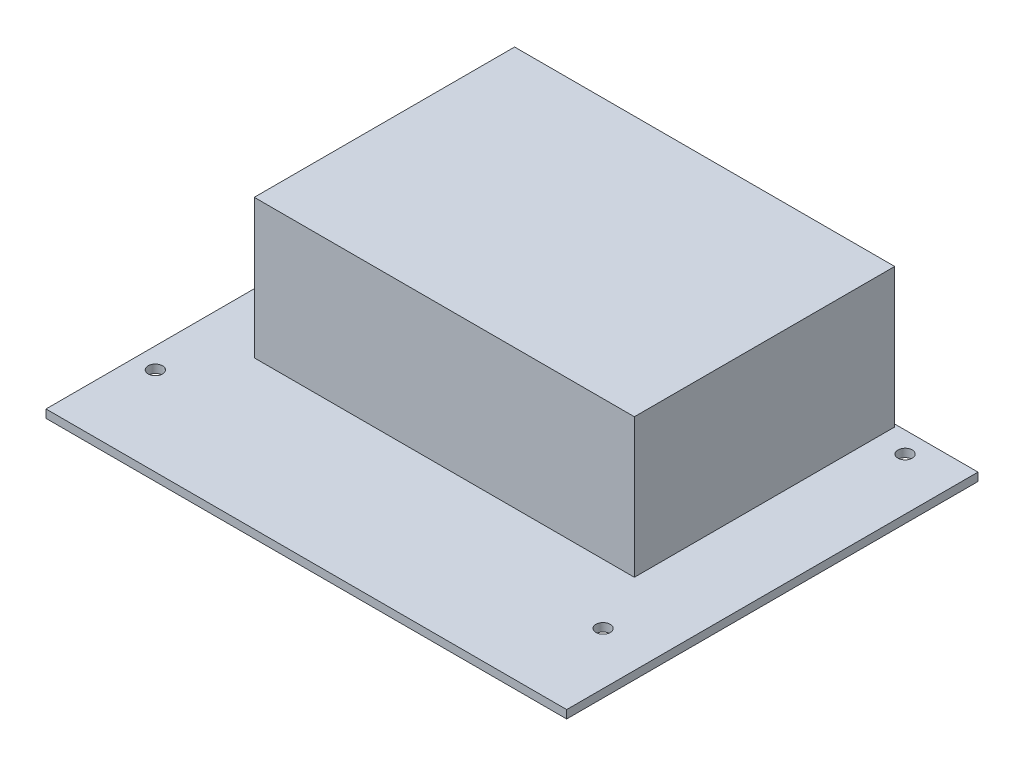
SolidWorks part; units mm, degrees
ref_plane "Front Plane" through (0, 0, 0) normal (0, 0, 1) x (1, 0, 0)
ref_plane "Top Plane" through (0, 0, 0) normal (0, 1, 0) x (1, 0, 0)
ref_plane "Right Plane" through (0, 0, 0) normal (1, 0, 0) x (0, 0, -1)
sketch "Sketch1" plane through (0, 0, 0) normal (0, 1, 0) x (1, 0, 0)
  line L1 (-50, -39.5) -> (50, -39.5)
  line L2 (-50, -39.5) -> (-50, 39.5)
  line L3 (-50, 39.5) -> (50, 39.5)
  line L4 (50, -39.5) -> (50, 39.5)
  line L5 (-50, -39.5) -> (50, 39.5) construction
  line L6 (-50, 39.5) -> (50, -39.5) construction
  circle A0 centre (-46, 35.5) radius 1.375
  circle A1 centre (40, 35.5) radius 1.375
  circle A2 centre (-46, -22.5) radius 1.375
  circle A3 centre (40, -22.5) radius 1.375
  point P0 (0, 0)
  dimension "D7" = 2.75
  dimension "D1" = 100
  dimension "D2" = 79
  dimension "D3" = 4
  dimension "D4" = 4
  dimension "D5" = 10
  dimension "D6" = 17
extrude "Boss-Extrude1" add sketch "Sketch1" along normal blind 1.57
sketch "Sketch2" plane through (0, 1.57, 0) normal (0, 1, 0) x (1, 0, 0)
  line L0 (-50, 39.5) -> (-50, -39.5) construction
  line L1 (-38.5, -11) -> (34.5, -11)
  line L2 (-38.5, -11) -> (-38.5, 39)
  line L3 (-38.5, 39) -> (34.5, 39)
  line L4 (34.5, -11) -> (34.5, 39)
  line L5 (-38.5, -11) -> (34.5, 39) construction
  line L6 (-38.5, 39) -> (34.5, -11) construction
  line L7 (50, 39.5) -> (-50, 39.5) construction
  point P0 (-2, 14)
  dimension "D1" = 50
  dimension "D2" = 73
  dimension "D3" = 11.5
  dimension "D4" = 0.5
extrude "Boss-Extrude2" add sketch "Sketch2" along normal blind 26.706
